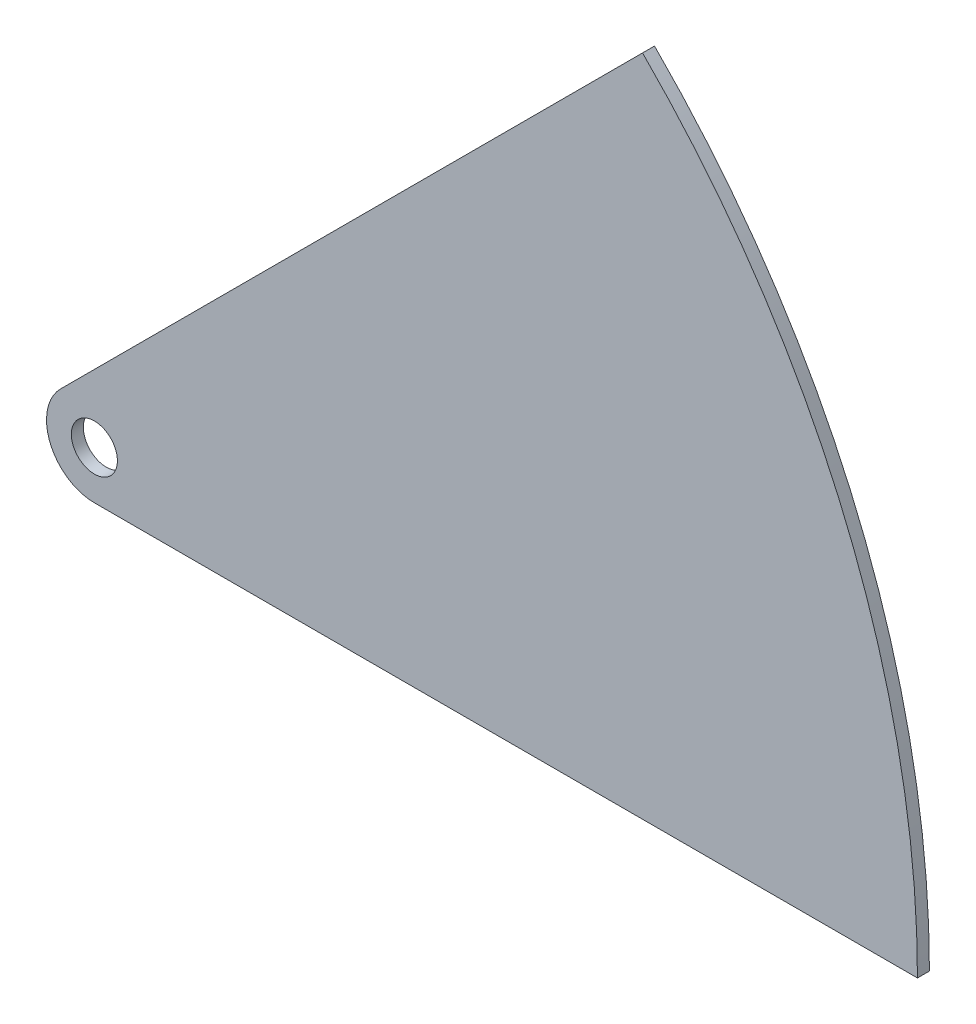
SolidWorks part; units mm, degrees
ref_plane "Front Plane" through (0, 0, 0) normal (0, 0, 1) x (1, 0, 0)
ref_plane "Top Plane" through (0, 0, 0) normal (0, 1, 0) x (1, 0, 0)
ref_plane "Right Plane" through (0, 0, 0) normal (1, 0, 0) x (0, 0, -1)
sketch "Sketch2" plane through (0, 0, 0) normal (0, 0, 1) x (1, 0, 0)
  line L7 (-8.9803, 8.9803) -> (145.4801, 163.4407)
  line L8 (218.44, -12.7) -> (0, -12.7)
  circle A1 centre (0, 0) radius 6.1087
  arc A2 (-8.9803, 8.9803) -> (0, -12.7) centre (0, 0) ccw
  arc A5 (218.44, -12.7) -> (145.4801, 163.4407) centre (-30.6605, -12.7) ccw
  point P5 (116.0801, 134.0406)
  point P6 (129.8665, 176.1023)
  point P11 (0, 0)
  point P13 (111.9012, 111.9012)
  dimension "D1" = 12.7
  dimension "D2" = 12.2174
  dimension "D3" = 218.44
  dimension "D4" = 45
  dimension "D6" = 218.44
extrude "Boss-Extrude1" add sketch "Sketch2" along normal blind 3.175
